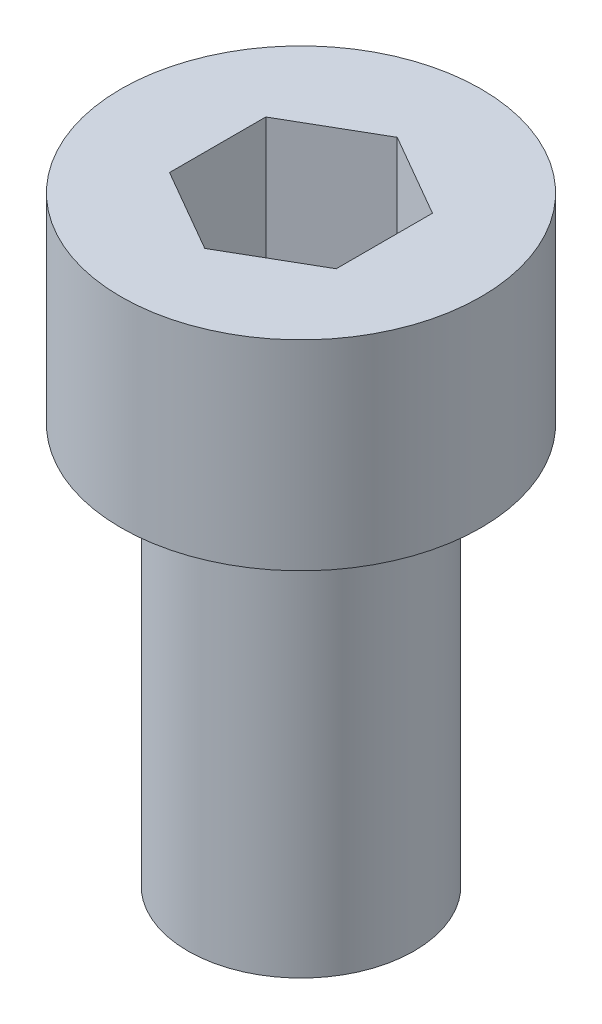
SolidWorks part; units mm, degrees
ref_plane "Front Plane" through (0, 0, 0) normal (0, 0, 1) x (1, 0, 0)
ref_plane "Top Plane" through (0, 0, 0) normal (0, 1, 0) x (1, 0, 0)
ref_plane "Right Plane" through (0, 0, 0) normal (1, 0, 0) x (0, 0, -1)
sketch "Sketch1" plane through (0, 0, 0) normal (0, 1, 0) x (1, 0, 0)
  circle A0 centre (184.7145, -125.2443) radius 2.7
  dimension "D1" = 5.4
extrude "Boss-Extrude1" add sketch "Sketch1" against normal blind 3
sketch "Sketch2" plane through (0, -3, 0) normal (0, -1, 0) x (1, 0, 0)
  circle A0 centre (184.7145, 125.2443) radius 1.6963
extrude "Boss-Extrude2" add sketch "Sketch2" along normal blind 6
sketch "Sketch3" plane through (0, 0, 0) normal (0, 1, 0) x (1, 0, 0)
  line L1 (184.7145, -123.8009) -> (183.4645, -124.5226)
  line L2 (183.4645, -124.5226) -> (183.4645, -125.966)
  line L3 (183.4645, -125.966) -> (184.7145, -126.6877)
  line L4 (184.7145, -126.6877) -> (185.9645, -125.966)
  line L5 (185.9645, -125.966) -> (185.9645, -124.5226)
  line L6 (185.9645, -124.5226) -> (184.7145, -123.8009)
  circle A0 centre (184.7145, -125.2443) radius 1.25 construction
  dimension "D1" = 2.5
extrude "Cut-Extrude1" cut sketch "Sketch3" against normal blind 2
